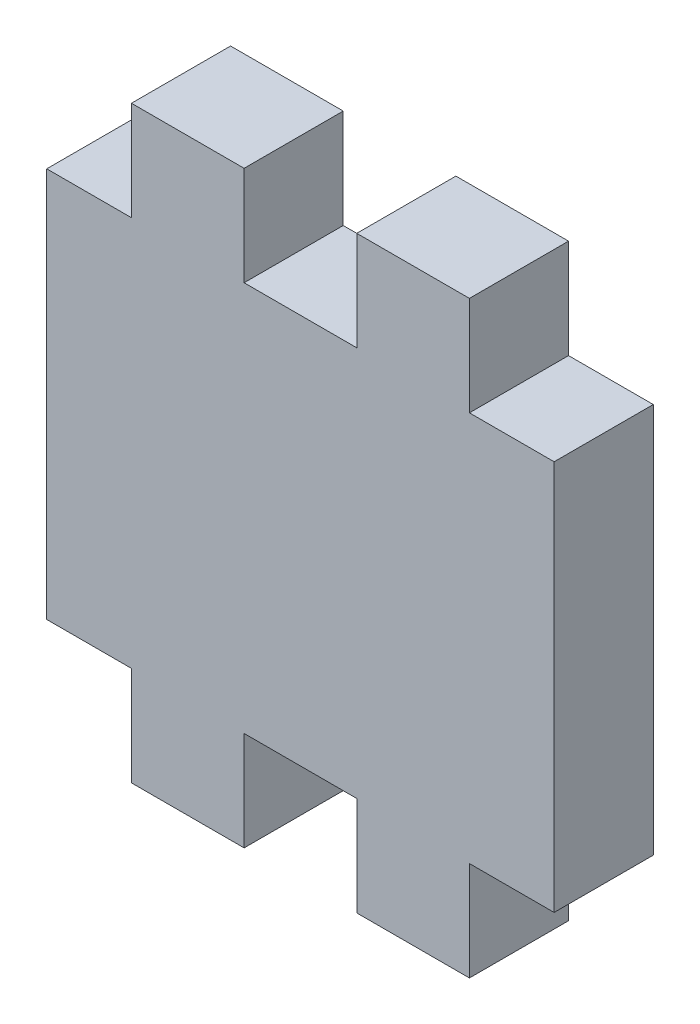
SolidWorks part; units mm, degrees
ref_plane "Front Plane" through (0, 0, 0) normal (0, 0, 1) x (1, 0, 0)
ref_plane "Top Plane" through (0, 0, 0) normal (0, 1, 0) x (1, 0, 0)
ref_plane "Right Plane" through (0, 0, 0) normal (1, 0, 0) x (0, 0, -1)
sketch "Sketch1" plane through (0, 0, 0) normal (0, 0, 1) x (1, 0, 0)
  line L0 (11.125, 24.794) -> (17.475, 24.794) construction
  line L1 (0, 0) -> (4.775, 0)
  line L2 (0, 0) -> (0, 22)
  line L3 (0, 22) -> (4.775, 22)
  line L4 (28.6, 0) -> (28.6, 22)
  line L6 (4.775, 22) -> (4.775, 27.588)
  line L7 (4.775, 27.588) -> (11.125, 27.588)
  line L8 (11.125, 22) -> (11.125, 27.588)
  line L10 (17.475, 22) -> (17.475, 27.588)
  line L11 (17.475, 27.588) -> (23.825, 27.588)
  line L12 (23.825, 22) -> (23.825, 27.588)
  line L13 (14.3, 0) -> (14.3, 24.794) construction
  line L14 (11.125, 22) -> (17.475, 22)
  line L15 (23.825, 22) -> (28.6, 22)
  line L16 (0, 11) -> (28.6, 11) construction
  line L17 (23.825, 0) -> (23.825, -5.588)
  line L18 (17.475, -5.588) -> (23.825, -5.588)
  line L19 (17.475, 0) -> (17.475, -5.588)
  line L20 (11.125, 0) -> (11.125, -5.588)
  line L21 (4.775, 0) -> (4.775, -5.588)
  line L22 (4.775, -5.588) -> (11.125, -5.588)
  line L23 (11.125, 0) -> (17.475, 0)
  line L24 (23.825, 0) -> (28.6, 0)
  point P17 (14.3, 22)
  point P28 (14.3, 0)
  dimension "D1" = 5.588
  dimension "D2" = 6.35
  dimension "D3" = 6.35
  dimension "D4" = 28.6
  dimension "D5" = 22
  dimension "D7" = 14.3
  dimension "D8" = 11
extrude "Boss-Extrude1" add sketch "Sketch1" along normal blind 5.588
